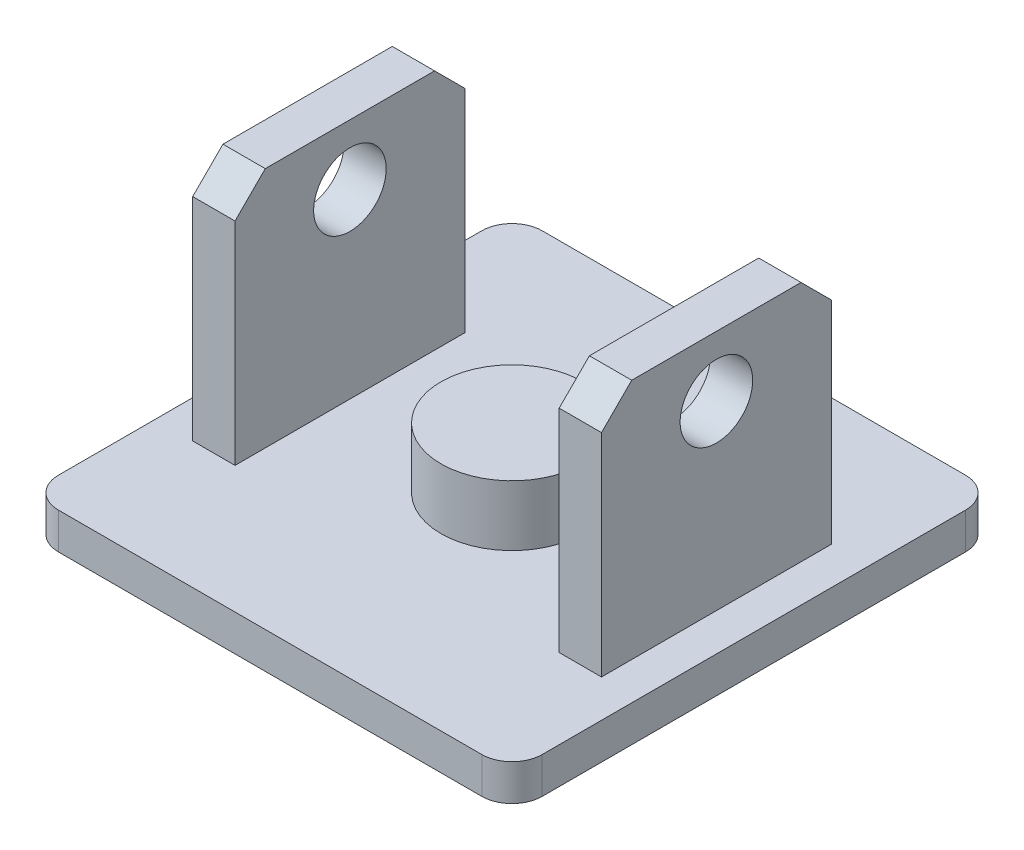
SolidWorks part; units mm, degrees
ref_plane "Front Plane" through (0, 0, 0) normal (0, 0, 1) x (1, 0, 0)
ref_plane "Top Plane" through (0, 0, 0) normal (0, 1, 0) x (1, 0, 0)
ref_plane "Right Plane" through (0, 0, 0) normal (1, 0, 0) x (0, 0, -1)
sketch "Sketch1" plane through (0, 0, 0) normal (0, 1, 0) x (1, 0, 0)
  line L1 (-20, 20) -> (20, 20)
  line L2 (-20, 20) -> (-20, -20)
  line L3 (-20, -20) -> (20, -20)
  line L4 (20, 20) -> (20, -20)
  line L5 (-20, 20) -> (20, -20) construction
  line L6 (-20, -20) -> (20, 20) construction
  point P0 (0, 0)
  dimension "D1" = 40
extrude "Boss-Extrude1" add sketch "Sketch1" along normal blind 3
sketch "Sketch2" plane through (0, 3, 0) normal (0, 1, 0) x (1, 0, 0)
  circle A0 centre (0, 0) radius 5.875
  dimension "D1" = 11.75
extrude "Boss-Extrude2" add sketch "Sketch2" along normal blind 5
sketch "Sketch3" plane through (0, 3, 0) normal (0, 1, 0) x (1, 0, 0)
  line L0 (5.875, 0) -> (20, 0) construction
  line L1 (20, -20) -> (20, 20) construction
  line L3 (13.4, 9.5) -> (16.9, 9.5)
  line L4 (13.4, 9.5) -> (13.4, -9.5)
  line L5 (13.4, -9.5) -> (16.9, -9.5)
  line L6 (16.9, 9.5) -> (16.9, -9.5)
  line L7 (13.4, 9.5) -> (16.9, -9.5) construction
  line L8 (13.4, -9.5) -> (16.9, 9.5) construction
  circle A0 centre (0, 0) radius 5.875 construction
  point P6 (15.15, 0)
  point P11 (0, 0)
  dimension "D1" = 19
  dimension "D2" = 3.1
  dimension "D3" = 3.5
extrude "Boss-Extrude3" add sketch "Sketch3" along normal blind 20
sketch "Sketch4" plane through (16.9, 0, 0) normal (1, 0, 0) x (0, 0, -1)
  line L0 (0, 3) -> (0, 18) construction
  line L1 (-9.5, 3) -> (9.5, 3) construction
  circle A0 centre (0, 18) radius 3
  dimension "D1" = 6
  dimension "D2" = 15
extrude "Cut-Extrude1" cut sketch "Sketch4" against normal up to next (3.5 mm away)
fillet "Fillet1" radius 2.5 4 edges at (20, 1.5, 20) (20, 1.5, -20) (-20, 1.5, 20) (-20, 1.5, -20)
mirror "Mirror1" about plane through (0, 0, 0) normal (1, 0, 0) of "Cut-Extrude1", "Boss-Extrude3"
chamfer "Chamfer1" distance 2.5 angle 45 4 edges at (-15.15, 23, 9.5) (-15.15, 23, -9.5) (15.15, 23, 9.5) (15.15, 23, -9.5)
